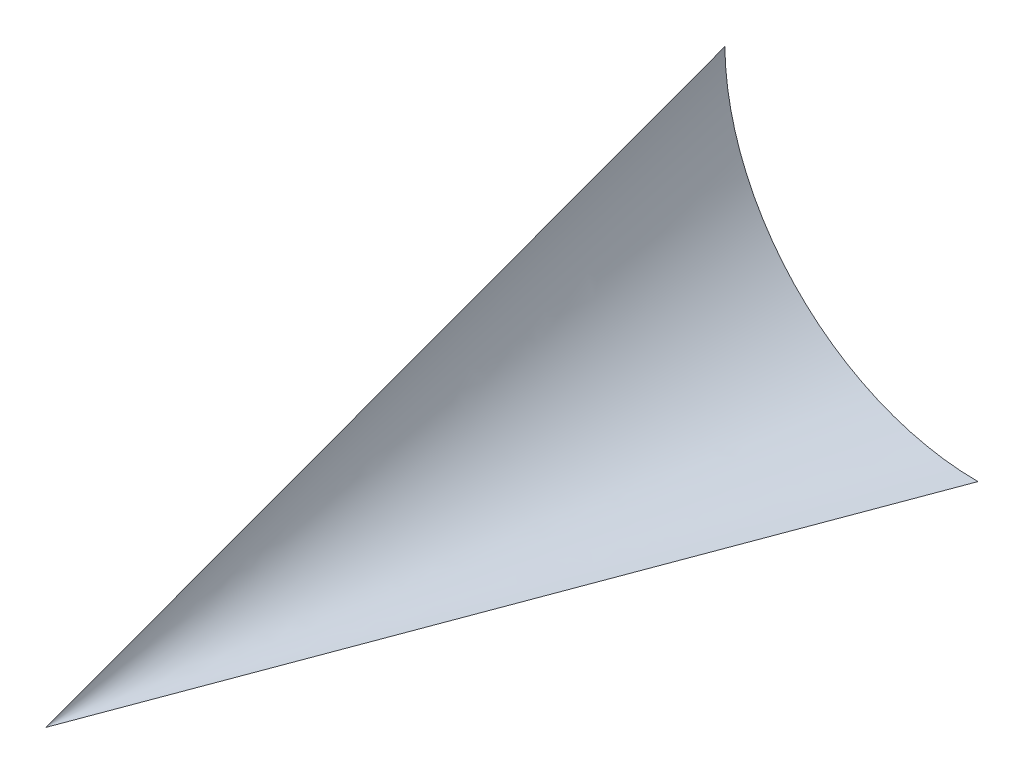
SolidWorks part; units mm, degrees
ref_plane "Plan de face" through (0, 0, 0) normal (0, 0, 1) x (1, 0, 0)
ref_plane "Plan de dessus" through (0, 0, 0) normal (0, 1, 0) x (1, 0, 0)
ref_plane "Plan de droite" through (0, 0, 0) normal (1, 0, 0) x (0, 0, -1)
sketch "Esquisse1" plane through (0, 0, 0) normal (0, 0, 1) x (1, 0, 0)
  line L0 (0, 55.1096) -> (0, 0)
  line L1 (0, 0) -> (55.7829, 0)
  arc A0 (0, 55.1096) -> (55.7829, 0) centre (55.7829, 55.7871) ccw
sketch "Esquisse2" plane through (0, 0, 0) normal (0, 1, 0) x (1, 0, 0)
  point P0 (0, -149.5769)
loft "Lissage1" add profiles "Esquisse2", "Esquisse1"
